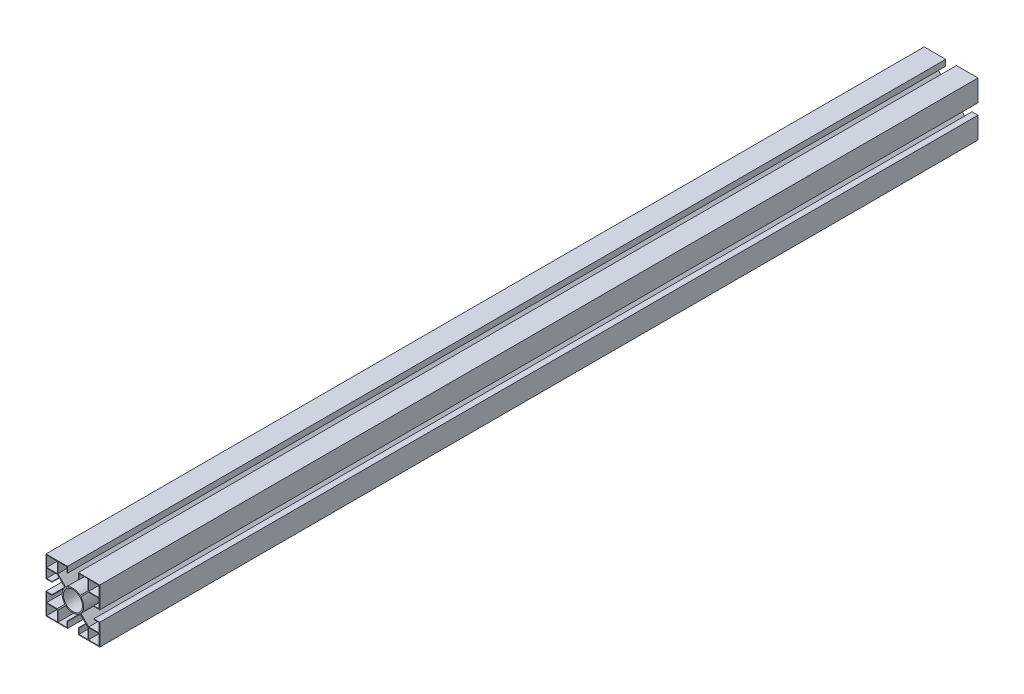
SolidWorks part; units mm, degrees
material "201.0-T7 Molde de fundição com isolamento (SS)"
ref_plane "Plano frontal" through (0, 0, 0) normal (0, 0, 1) x (1, 0, 0)
ref_plane "Plano superior" through (0, 0, 0) normal (0, 1, 0) x (1, 0, 0)
ref_plane "Plano direito" through (0, 0, 0) normal (1, 0, 0) x (0, 0, -1)
sketch "Esboço1" plane through (0, 0, 0) normal (0, 0, 1) x (1, 0, 0)
  line L1 (-6.0006, -6.7077) -> (-12.5, -13.2071)
  line L2 (22.5, -22.5) -> (22.5, -4.5)
  line L3 (22.5, 22.5) -> (4.5, 22.5)
  line L4 (-22.5, -22.5) -> (-22.5, -4.5)
  line L5 (-5, -22) -> (-5, -17.5)
  line L6 (-5, -22) -> (-22, -22)
  line L7 (-22.5, 22.5) -> (-12.5, 22.5)
  line L8 (-22.5, 22.5) -> (-22.5, 12.5)
  line L9 (-22, 12.5) -> (-13.2071, 12.5)
  line L10 (-12.5, 22) -> (-12.5, 13.2071)
  line L11 (22.5, 22.5) -> (12.5, 22.5)
  line L12 (22.5, 22.5) -> (22.5, 12.5)
  line L13 (22.5, 12.5) -> (13.2071, 12.5)
  line L14 (12.5, 22.5) -> (12.5, 13.2071)
  line L15 (-22, -22) -> (-22, -5)
  line L16 (-22, -5) -> (-17.5, -5)
  line L17 (-22, 22) -> (-22, 13)
  line L18 (6.7077, 6.0006) -> (13.2071, 12.5)
  line L19 (6.0006, 6.7077) -> (12.5, 13.2071)
  line L20 (-6.7077, 6.0006) -> (-13.2071, 12.5)
  line L21 (-22, 13) -> (-13, 13)
  line L22 (-17.5, -5) -> (-17.5, -4.5)
  line L23 (-13, 22) -> (-13, 13)
  line L24 (-22.5, 12.5) -> (-12.5, 12.5) construction
  line L25 (-22, 22) -> (-13, 22)
  line L26 (22, 22) -> (13, 22)
  line L27 (13, 22) -> (13, 13)
  line L28 (22, 13) -> (13, 13)
  line L29 (22, 22) -> (22, 13)
  line L30 (-6.0006, 6.7077) -> (-12.5, 13.2071)
  line L31 (-12.5, 22.5) -> (-12.5, 12.5) construction
  line L32 (12.5, 22.5) -> (12.5, 12.5) construction
  line L33 (22.5, 12.5) -> (12.5, 12.5) construction
  line L34 (-6.7077, -6.0006) -> (-13.2071, -12.5)
  line L35 (6.0006, -6.7077) -> (12.5, -13.2071)
  line L36 (6.7077, -6.0006) -> (13.2071, -12.5)
  line L37 (12.5, -22) -> (12.5, -13.2071)
  line L38 (22, -22) -> (13, -22)
  line L39 (13, -22) -> (13, -13)
  line L40 (22, -22) -> (22, -13)
  line L41 (22, -13) -> (13, -13)
  line L42 (22, -12.5) -> (13.2071, -12.5)
  line L43 (-12.5, -22) -> (-12.5, -13.2071)
  line L44 (-13, -22) -> (-13, -13)
  line L45 (-22, -22) -> (-22, -13)
  line L46 (-22, -22) -> (-13, -22)
  line L47 (22.5, -22.5) -> (4.5, -22.5)
  line L48 (-22.5, -12.5) -> (-13.2071, -12.5)
  line L49 (-22, -13) -> (-13, -13)
  line L50 (-4.5, 22.5) -> (-4.5, 17.5)
  line L51 (4.5, 22.5) -> (4.5, 17.5)
  line L52 (-4.5, 22.5) -> (-22.5, 22.5)
  line L53 (-4.5, -22.5) -> (-4.5, -17.5)
  line L54 (4.5, -22.5) -> (4.5, -17.5)
  line L55 (-4.5, -22.5) -> (-22.5, -22.5)
  line L56 (-22.5, 4.5) -> (-17.5, 4.5)
  line L57 (-22.5, -4.5) -> (-17.5, -4.5)
  line L59 (-22.5, 4.5) -> (-22.5, 22.5)
  line L60 (22.5, -4.5) -> (17.5, -4.5)
  line L61 (22.5, 4.5) -> (17.5, 4.5)
  line L62 (22.5, 4.5) -> (22.5, 22.5)
  line L63 (-4.5, -17.5) -> (-5, -17.5)
  line L64 (-5, 22) -> (-5, 17.5)
  line L65 (-5, 22) -> (-22.5, 22)
  line L66 (-22, 5) -> (-22, 22.5)
  line L67 (-22, 5) -> (-17.5, 5)
  line L68 (-5, 17.5) -> (-4.5, 17.5)
  line L69 (-17.5, 4.5) -> (-17.5, 5)
  line L70 (22, -5) -> (17.5, -5)
  line L71 (22, -22) -> (22, -5)
  line L72 (22, -22) -> (5, -22)
  line L73 (5, -22) -> (5, -17.5)
  line L74 (4.5, -17.5) -> (5, -17.5)
  line L75 (17.5, -5) -> (17.5, -4.5)
  line L76 (22.5, 22) -> (5, 22)
  line L77 (5, 22) -> (5, 17.5)
  line L78 (22, 5) -> (17.5, 5)
  line L79 (22, 5) -> (22, 22.5)
  line L80 (4.5, 17.5) -> (5, 17.5)
  line L81 (17.5, 5) -> (17.5, 4.5)
  circle A0 centre (0, 0) radius 8
  arc A1 (6.7077, -6.0006) -> (6.7077, 6.0006) centre (0, 0) ccw
  circle A2 centre (0, 0) radius 9 construction
  arc A3 (6.0006, 6.7077) -> (-6.0006, 6.7077) centre (0, 0) ccw
  arc A4 (-6.7077, 6.0006) -> (-6.7077, -6.0006) centre (0, 0) ccw
  arc A5 (-6.0006, -6.7077) -> (6.0006, -6.7077) centre (0, 0) ccw
  point P0 (0, 0)
  dimension "D9" = 8
  dimension "D1" = 45
  dimension "D2" = 8
  dimension "D3" = 0.5
  dimension "D4" = 0.5
  dimension "D5" = 0.5
  dimension "D10" = 5
  dimension "D11" = 5
  dimension "D12" = 8
  dimension "D13" = 5
  dimension "D14" = 8
  dimension "D15" = 5
  dimension "D6" = 0.5
  dimension "D7" = 0.5
extrude "Ressalto-extrusão4" add sketch "Esboço1" along normal blind 734.5 contours L1 A5 L35 L37 L72 L39 L41 L71 L42 L36 A1 L18 L13 L79 L28 L27 L76 L14 L19 A3 L30 L10 L65 L23 L21 L66 L9 L20 A4 L34 L48 L15 L49 L44 L6 L43 A0 | L53 L63 L5 L6 L15 L48 L4 L55 | L57 L4 L48 L15 L16 L22 | L78 L81 L61 L62 L13 L79 | L79 L13 L62 L76 L29 | L26 L79 L11 L14 L76 | L79 L76 L12 L3 | L51 L80 L77 L76 L14 L3 | L56 L69 L67 L66 L17 L65 L59 | L64 L68 L50 L52 L66 L25 L65 | L65 L66 L7 L8
